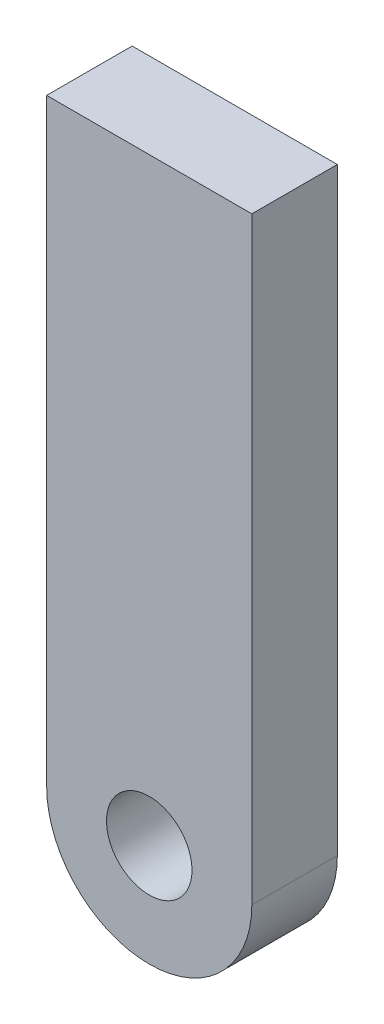
SolidWorks part; units mm, degrees
ref_plane "Front Plane" through (0, 0, 0) normal (0, 0, 1) x (1, 0, 0)
ref_plane "Top Plane" through (0, 0, 0) normal (0, 1, 0) x (1, 0, 0)
ref_plane "Right Plane" through (0, 0, 0) normal (1, 0, 0) x (0, 0, -1)
sketch "Sketch1" plane through (0, 0, 0) normal (0, 0, 1) x (1, 0, 0)
  line L1 (-7.62, 0) -> (-7.62, 44.45)
  line L2 (7.62, 0) -> (7.62, 44.45)
  line L3 (-7.62, 44.45) -> (7.62, 44.45)
  arc A0 (-7.62, 0) -> (7.62, 0) centre (0, 0) ccw
  circle A1 centre (0, 0) radius 3.175
  dimension "D1" = 44.45
extrude "Boss-Extrude1" add sketch "Sketch1" along normal blind 6.35
